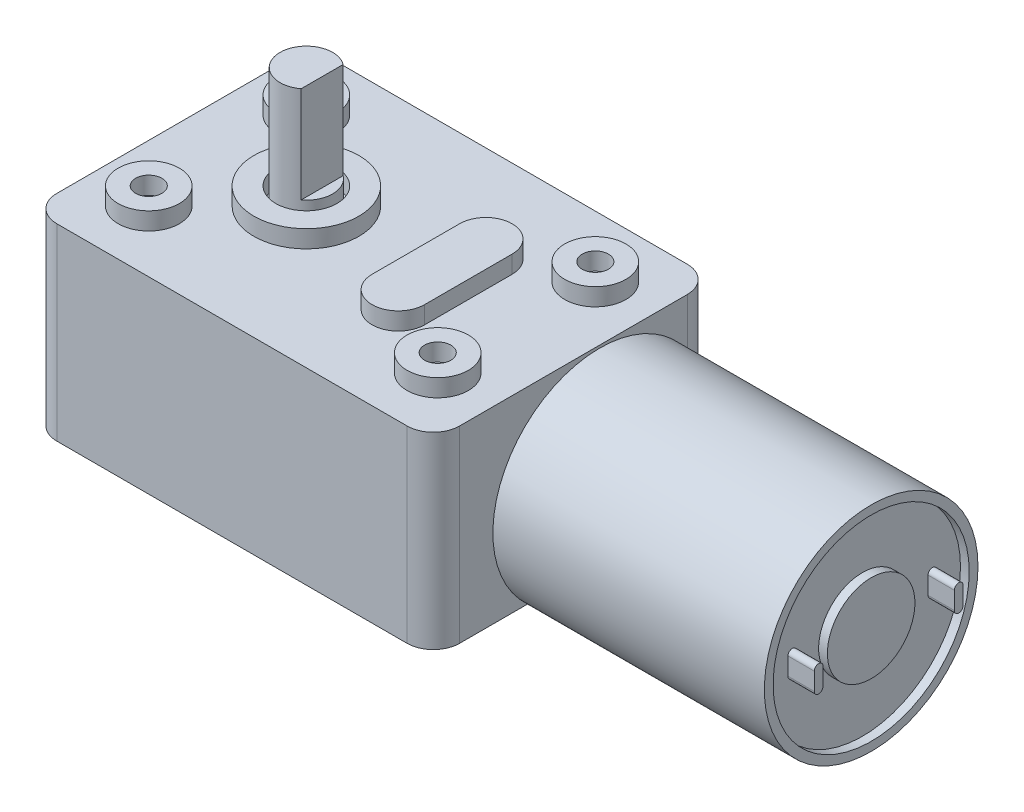
SolidWorks part; units mm, degrees
ref_plane "Front Plane" through (0, 0, 0) normal (0, 0, 1) x (1, 0, 0)
ref_plane "Top Plane" through (0, 0, 0) normal (0, 1, 0) x (1, 0, 0)
ref_plane "Right Plane" through (0, 0, 0) normal (1, 0, 0) x (0, 0, -1)
sketch "Sketch1" plane through (0, 0, 0) normal (0, 1, 0) x (1, 0, 0)
  line L1 (-23, -16) -> (23, -16)
  line L2 (-23, -16) -> (-23, 16)
  line L3 (-23, 16) -> (23, 16)
  line L4 (23, -16) -> (23, 16)
  line L5 (0, 16) -> (0, -16) construction
  line L6 (-23, 0) -> (23, 0) construction
  point P0 (0, 0)
  dimension "D1" = 32
  dimension "D2" = 46
extrude "Boss-Extrude1" add sketch "Sketch1" along normal blind 21.5
fillet "Fillet1" radius 3 4 edges at (-23, 10.75, -16) (23, 10.75, -16) (23, 10.75, 16) (-23, 10.75, 16)
sketch "Sketch2" plane through (0, 21.5, 0) normal (0, 1, 0) x (1, 0, 0)
  line L0 (8, 5) -> (8, -5) construction
  line L1 (11, 5) -> (11, -5)
  line L2 (5, 5) -> (5, -5)
  line L3 (-23, 13) -> (-23, -13) construction
  line L4 (23, -13) -> (23, 13) construction
  circle A0 centre (-16.5, 9) radius 1.5
  circle A1 centre (-7.5, 0) radius 3.5
  arc A2 (11, 5) -> (5, 5) centre (8, 5) ccw
  arc A3 (5, -5) -> (11, -5) centre (8, -5) ccw
  circle A4 centre (-16.5, 9) radius 3.5
  circle A5 centre (16.5, 9) radius 3.5
  circle A6 centre (16.5, 9) radius 1.5
  circle A7 centre (16.5, -9) radius 3.5
  circle A8 centre (16.5, -9) radius 1.5
  circle A9 centre (-16.5, -9) radius 3.5
  circle A10 centre (-16.5, -9) radius 1.5
  circle A11 centre (-7.5, 0) radius 6
  point P6 (8, 0)
  dimension "D1" = 3
  dimension "D2" = 7
  dimension "D10" = 7
  dimension "D11" = 12
  dimension "D3" = 6.5
  dimension "D4" = 9
  dimension "D7" = 33
  dimension "D8" = 18
  dimension "D9" = 15.5
  dimension "D12" = 6
  dimension "D13" = 10
  dimension "D14" = 15
  dimension "D5" = 2
  dimension "D6" = 2
extrude "Boss-Extrude2" add sketch "Sketch2" along normal blind 2
sketch "Sketch3" plane through (0, 21.5, 0) normal (0, 1, 0) x (1, 0, 0)
  circle A0 centre (-7.5, 0) radius 3
  dimension "D1" = 6
extrude "Boss-Extrude3" add sketch "Sketch3" along normal blind 13.7
sketch "Sketch4" plane through (0, 35.2, 0) normal (0, 1, 0) x (1, 0, 0)
  line L0 (-5.7, 2.4) -> (-5.7, -2.4)
  circle A0 centre (-7.5, 0) radius 3 construction
  circle A2 centre (-7.5, 0) radius 3
  circle A3 centre (-7.5, 0) radius 3
  circle M3 centre (-7.5, 0) radius 3
  dimension "D2" = 1.8
  dimension "D1" = 0
extrude "Cut-Extrude1" cut sketch "Sketch4" against normal blind 11 contours L0 M3
sketch "Sketch6" plane through (23, 0, 0) normal (1, 0, 0) x (0, 0, -1)
  line L0 (-13, 21.5) -> (13, 21.5) construction
  circle A0 centre (3, 9) radius 12.2
  point P4 (0, 21.5)
  dimension "D1" = 24.4
  dimension "D2" = 3
  dimension "D3" = 12.5
extrude "Boss-Extrude5" add sketch "Sketch6" along normal blind 31
sketch "Sketch7" plane through (54, 0, 0) normal (1, 0, 0) x (0, 0, -1)
  circle A0 centre (3, 9) radius 11.2
  circle A1 centre (3, 9) radius 12.2
  circle A2 centre (3, 9) radius 12.2
  circle A3 centre (3, 9) radius 5
  dimension "D3" = 10
  dimension "D1" = 0
  dimension "D2" = 1
extrude "Cut-Extrude2" cut sketch "Sketch7" against normal blind 1 contours A0 A3
sketch "Sketch8" plane through (53, 0, 0) normal (1, 0, 0) x (0, 0, -1)
  line L0 (-5, 8) -> (-5, 10) construction
  line L1 (-5.5, 8) -> (-5.5, 10)
  line L2 (-4.5, 8) -> (-4.5, 10)
  line L3 (3, 9) -> (-1.8529, 9) construction
  arc A0 (-5.5, 8) -> (-4.5, 8) centre (-5, 8) ccw
  arc A1 (-4.5, 10) -> (-5.5, 10) centre (-5, 10) ccw
  point P2 (-5, 9)
  dimension "D1" = 1
  dimension "D2" = 2
  dimension "D3" = 8
extrude "Boss-Extrude6" add sketch "Sketch8" along normal blind 3
pattern_circular "CirPattern1" count 2 over 360 about axis through (0, 9, -3) along (1, 0, 0) of "Boss-Extrude6"
